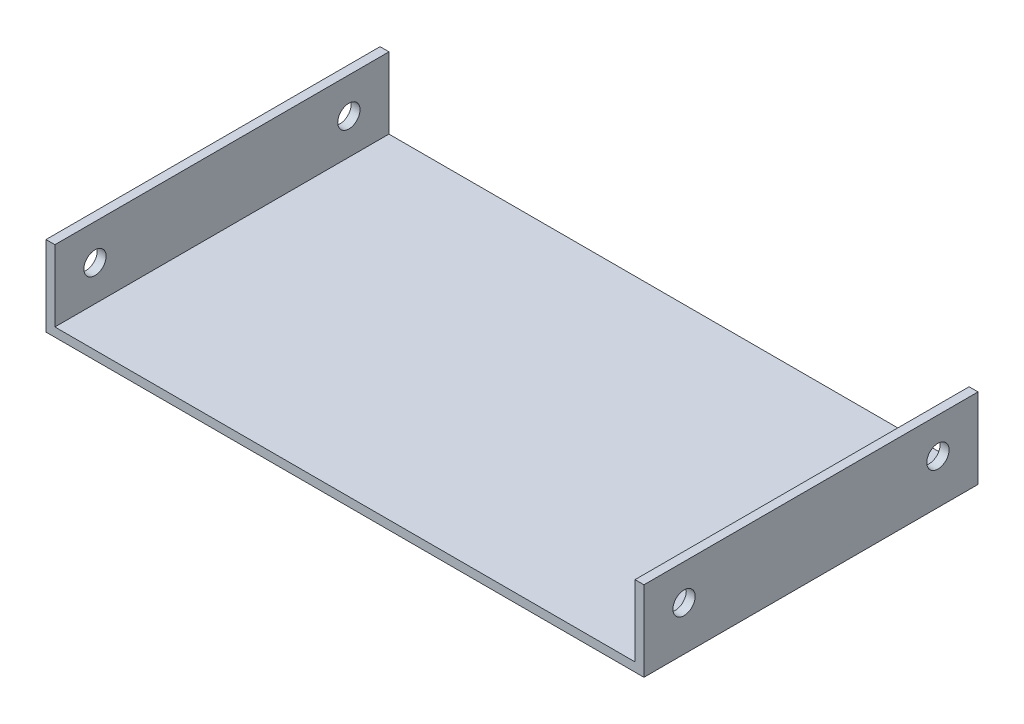
SolidWorks part; units mm, degrees
material "Liga 1060"
ref_plane "Plano frontal" through (0, 0, 0) normal (0, 0, 1) x (1, 0, 0)
ref_plane "Plano superior" through (0, 0, 0) normal (0, 1, 0) x (1, 0, 0)
ref_plane "Plano direito" through (0, 0, 0) normal (1, 0, 0) x (0, 0, -1)
sketch "Esboço1" plane through (0, 0, 0) normal (0, 1, 0) x (1, 0, 0)
  line L1 (-65.125, -37.5) -> (65.125, -37.5)
  line L2 (-65.125, -37.5) -> (-65.125, 37.5)
  line L3 (-65.125, 37.5) -> (65.125, 37.5)
  line L4 (65.125, -37.5) -> (65.125, 37.5)
  line L5 (-65.125, -37.5) -> (65.125, 37.5) construction
  line L6 (-65.125, 37.5) -> (65.125, -37.5) construction
  point P1 (0, 0)
  dimension "D1" = 130.25
  dimension "D2" = 75
extrude "Ressalto-extrusão1" add sketch "Esboço1" along normal blind 2
sketch "Esboço2" plane through (65.125, 0, 0) normal (1, 0, 0) x (0, 0, -1)
  line L0 (-37.5, 2) -> (-37.5, 0) construction
  line L1 (37.5, 0) -> (-37.5, 0)
  line L2 (37.5, 0) -> (37.5, 18)
  line L3 (37.5, 18) -> (-37.5, 18)
  line L4 (-37.5, 0) -> (-37.5, 18)
  dimension "D1" = 18
extrude "Ressalto-extrusão2" add sketch "Esboço2" along normal blind 2
mirror "Espelhar1" about plane through (0, 0, 0) normal (1, 0, 0) of "Ressalto-extrusão2"
fillet "Filete1" [suppressed] radius 5
sketch "Esboço3" plane through (-67.125, 0, 0) normal (-1, 0, 0) x (0, 0, 1)
  line L0 (-37.5, 18) -> (37.5, 18) construction
  line L1 (-37.5, 0) -> (-37.5, 18) construction
  line L2 (0, -8.8) -> (0, 8.8) construction
  circle A0 centre (-28.5, 10) radius 2.5
  circle A1 centre (28.5, 10) radius 2.5
  dimension "D1" = 5
  dimension "D2" = 8
  dimension "D3" = 9
extrude "Corte-extrusão1" cut sketch "Esboço3" against normal through all
sketch "Esboço4" plane through (0, 2, 0) normal (0, 1, 0) x (1, 0, 0)
  circle A0 centre (0, 0) radius 20
  dimension "D1" = 40
sketch "Esboço13" plane through (0, 0, 0) normal (0, -1, 0) x (1, 0, 0)
  circle A0 centre (-15.7, -24.7) radius 1.75 construction
  circle A1 centre (-24.7, 15.7) radius 1.75 construction
  circle A2 centre (15.7, 24.7) radius 1.75 construction
  circle A3 centre (24.7, -15.7) radius 1.75 construction
  circle A4 centre (-15.7, -24.7) radius 1.75
  circle A5 centre (-24.7, 15.7) radius 1.75
  circle A6 centre (15.7, 24.7) radius 1.75
  circle A7 centre (24.7, -15.7) radius 1.75
extrude "Corte-extrusão4" [suppressed] cut sketch "Esboço13" against normal through all
sketch "Esboço15" [suppressed] plane through (0, 0, 0) normal (0, 0, 1) x (1, 0, 0)
  line L0 (31.2, 18) -> (20, 2)
  line L1 (20, 2) -> (-20, 2) construction
rib "Nervura1" [suppressed] sketch "Esboço15" sketch "Esboço15" thickness 20 extrusion direction parallel to sketch draft on no parameters "D1"=20
mirror "Espelhar2" [suppressed] about plane through (0, 0, 0) normal (1, 0, 0)
sketch "Esboço18" plane through (0, 0, 0) normal (0, -1, 0) x (1, 0, 0)
  line L0 (67.125, 37.5) -> (67.125, -37.5) construction
  circle A0 centre (20.075, 0) radius 7.5
  dimension "D2" = 15
  dimension "D1" = 47.05
extrude "Corte-extrusão5" [suppressed] cut sketch "Esboço18" against normal blind 10
